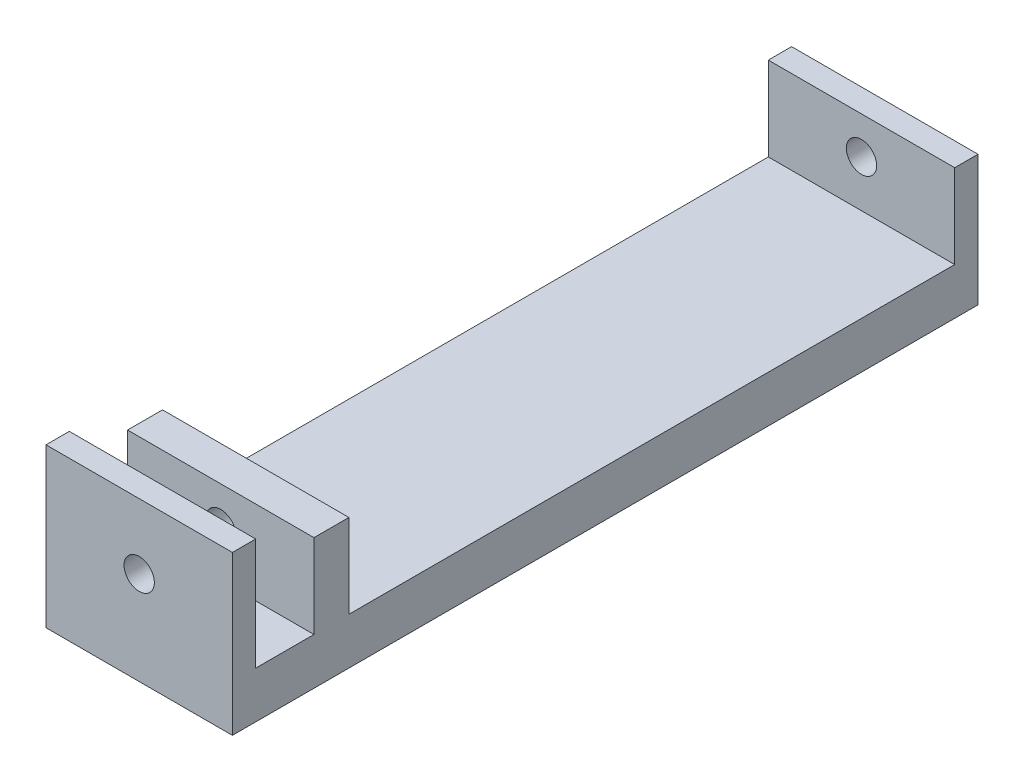
SolidWorks part; units mm, degrees
ref_plane "Front Plane" through (0, 0, 0) normal (0, 0, 1) x (1, 0, 0)
ref_plane "Top Plane" through (0, 0, 0) normal (0, 1, 0) x (1, 0, 0)
ref_plane "Right Plane" through (0, 0, 0) normal (1, 0, 0) x (0, 0, -1)
sketch "Sketch1" plane through (0, 0, 0) normal (1, 0, 0) x (0, 0, -1)
  line L0 (0, 20) -> (0, 68)
  line L1 (0, 0) -> (320, 0)
  line L2 (0, 0) -> (0, 20)
  line L3 (10, 20) -> (310, 20)
  line L4 (320, 0) -> (320, 20)
  line L5 (0, 0) -> (160, 10) construction
  line L6 (160, 10) -> (320, 0) construction
  line L7 (0, 68) -> (10, 68)
  line L8 (10, 68) -> (10, 20)
  line L9 (320, 20) -> (320, 56)
  line L10 (320, 56) -> (310, 56)
  line L11 (310, 56) -> (310, 20)
  line L12 (0, 20) -> (10, 20) construction
  line L13 (0, 20) -> (160, 10) construction
  line L14 (310, 20) -> (320, 20) construction
  line L15 (160, 10) -> (320, 20) construction
  line L17 (35, 20) -> (50, 20)
  line L18 (35, 20) -> (35, 56)
  line L19 (35, 56) -> (50, 56)
  line L20 (50, 20) -> (50, 56)
  line L21 (35, 20) -> (50, 56) construction
  line L22 (35, 56) -> (50, 20) construction
  point P4 (160, 10)
  point P17 (42.5, 38)
  dimension "D1" = 10
  dimension "D2" = 10
  dimension "D3" = 20
  dimension "D4" = 56
  dimension "D5" = 68
  dimension "D6" = 320
  dimension "D7" = 15
  dimension "D8" = 25
extrude "Boss-Extrude1" add sketch "Sketch1" along normal blind 80 contours L3 L20 L19 L18 | L10 L11 L3 L8 L7 L0 L2 L1 L4 L9
sketch "Sketch2" plane through (0, 0, -320) normal (0, 0, -1) x (-1, 0, 0)
  line L0 (-80, 0) -> (0, 0) construction
  circle A0 centre (-40, 40) radius 6.5
  point P4 (0, 0)
  point P5 (-40, 0)
  dimension "D1" = 40
  dimension "D2" = 13
extrude "Cut-Extrude1" cut sketch "Sketch2" against normal through all
